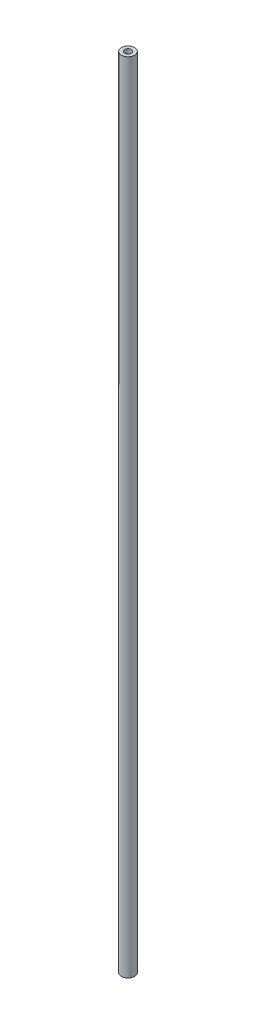
SolidWorks part; units mm, degrees
ref_plane "Front Plane" through (0, 0, 0) normal (0, 0, 1) x (1, 0, 0)
ref_plane "Top Plane" through (0, 0, 0) normal (0, 1, 0) x (1, 0, 0)
ref_plane "Right Plane" through (0, 0, 0) normal (1, 0, 0) x (0, 0, -1)
sketch "Sketch1" plane through (0, 0, 0) normal (0, 1, 0) x (1, 0, 0)
  circle A0 centre (0, 0) radius 12.7
  circle A1 centre (0, 0) radius 25.4
  dimension "D1" = 25.4
  dimension "D2" = 50.8
extrude "Boss-Extrude1" add sketch "Sketch1" along normal blind 3070.098
